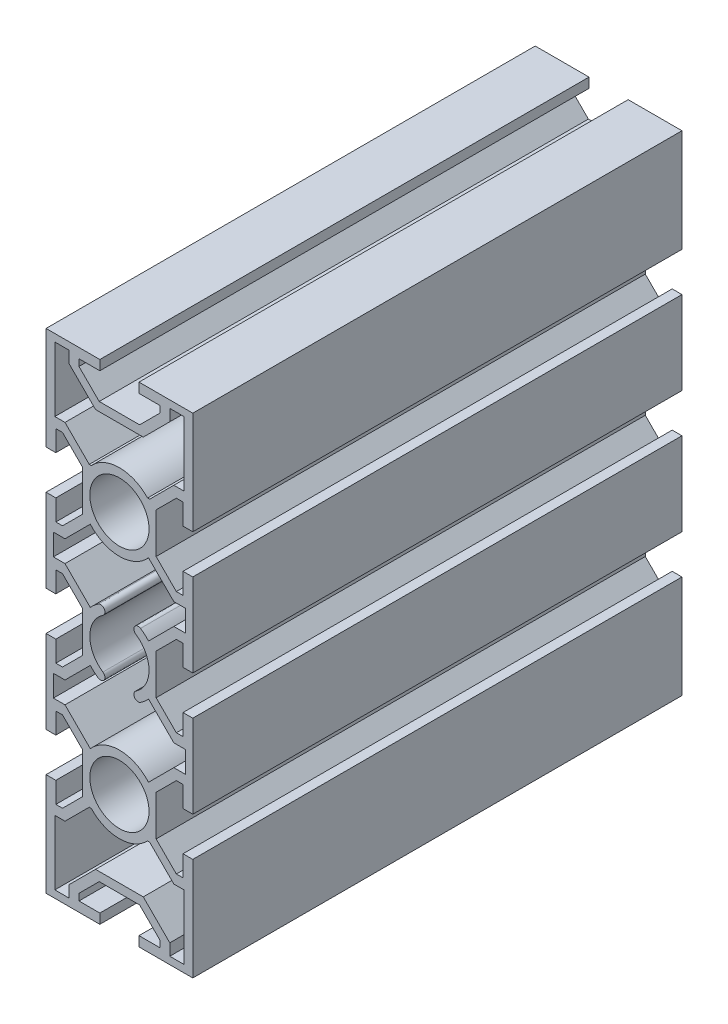
SolidWorks part; units mm, degrees
ref_plane "Front Plane" through (0, 0, 0) normal (0, 0, 1) x (1, 0, 0)
ref_plane "Top Plane" through (0, 0, 0) normal (0, 1, 0) x (1, 0, 0)
ref_plane "Right Plane" through (0, 0, 0) normal (1, 0, 0) x (0, 0, -1)
sketch "MB1-2" plane through (0, 0, 0) normal (0, 0, 1) x (1, 0, 0)
  line L134 (5.7482, -30.3461) -> (6.1691, -30.3461)
  line L135 (-6.1691, -30.3461) -> (-5.7482, -30.3461)
  line L136 (6.1691, 30.3461) -> (5.7482, 30.3461)
  line L137 (-5.7482, 30.3461) -> (-6.1691, 30.3461)
  line L138 (-13, -33.2657) -> (-11.6343, -33.2657)
  line L139 (-11.6343, -16.7343) -> (-13, -16.7343)
  line L140 (-13, -8.2657) -> (-11.6343, -8.2657)
  line L141 (-11.6343, 8.2657) -> (-13, 8.2657)
  line L142 (-13, 16.7343) -> (-11.6343, 16.7343)
  line L143 (-11.6343, 33.2657) -> (-13, 33.2657)
  line L144 (-8.2657, 48) -> (-8.2657, 46.6343)
  line L145 (8.2657, 46.6343) -> (8.2657, 48)
  line L146 (13, 33.2657) -> (11.6343, 33.2657)
  line L147 (11.6343, 16.7343) -> (13, 16.7343)
  line L148 (13, 8.2657) -> (11.6343, 8.2657)
  line L149 (11.6343, -8.2657) -> (13, -8.2657)
  line L150 (13, -16.7343) -> (11.6343, -16.7343)
  line L151 (11.6343, -33.2657) -> (13, -33.2657)
  line L152 (8.2657, -48) -> (8.2657, -46.6343)
  line L153 (-8.2657, -46.6343) -> (-8.2657, -48)
  line L154 (-13.2, -35.3) -> (-13.2, -48.5)
  line L155 (-13.2, -48.5) -> (-10.3, -48.5)
  line L156 (-10.3, -48.5) -> (-10.3, -46.123)
  line L157 (-10.3, -46.123) -> (-4.877, -40.7)
  line L158 (-4.877, -40.7) -> (4.877, -40.7)
  line L159 (4.877, -40.7) -> (10.3, -46.123)
  line L160 (10.3, -46.123) -> (10.3, -48.5)
  line L161 (10.3, -48.5) -> (13.2, -48.5)
  line L162 (13.2, -48.5) -> (13.2, -35.3)
  line L163 (13.2, -35.3) -> (11.123, -35.3)
  line L164 (11.123, -35.3) -> (6.1691, -30.3461)
  line L165 (-6.1691, -30.3461) -> (-11.123, -35.3)
  line L166 (-11.123, -35.3) -> (-13.2, -35.3)
  line L167 (6.1691, 30.3461) -> (11.123, 35.3)
  line L168 (11.123, 35.3) -> (13.2, 35.3)
  line L169 (13.2, 35.3) -> (13.2, 48.5)
  line L170 (13.2, 48.5) -> (10.3, 48.5)
  line L171 (10.3, 48.5) -> (10.3, 46.123)
  line L172 (10.3, 46.123) -> (4.877, 40.7)
  line L173 (4.877, 40.7) -> (-4.877, 40.7)
  line L174 (-4.877, 40.7) -> (-10.3, 46.123)
  line L175 (-10.3, 46.123) -> (-10.3, 48.5)
  line L176 (-10.3, 48.5) -> (-13.2, 48.5)
  line L177 (-13.2, 48.5) -> (-13.2, 35.3)
  line L178 (-13.2, 35.3) -> (-11.123, 35.3)
  line L179 (-11.123, 35.3) -> (-6.1691, 30.3461)
  line L180 (-11.123, -14.7) -> (-5.947, -19.876)
  line L181 (5.947, -19.876) -> (11.123, -14.7)
  line L182 (11.123, -14.7) -> (13.5, -14.7)
  line L183 (13.5, -14.7) -> (13.5, -10.3)
  line L184 (13.5, -10.3) -> (11.123, -10.3)
  line L185 (11.123, -10.3) -> (5.947, -5.124)
  line L186 (5.947, 5.124) -> (11.123, 10.3)
  line L187 (11.123, 10.3) -> (13.5, 10.3)
  line L188 (13.5, 10.3) -> (13.5, 14.7)
  line L189 (13.5, 14.7) -> (11.123, 14.7)
  line L190 (11.123, 14.7) -> (5.947, 19.876)
  line L191 (-5.947, 19.876) -> (-11.123, 14.7)
  line L192 (-11.123, 14.7) -> (-13.5, 14.7)
  line L193 (-13.5, 14.7) -> (-13.5, 10.3)
  line L194 (-13.5, 10.3) -> (-11.123, 10.3)
  line L195 (-11.123, 10.3) -> (-5.947, 5.124)
  line L196 (-5.947, -5.124) -> (-11.123, -10.3)
  line L197 (-11.123, -10.3) -> (-13.5, -10.3)
  line L198 (-13.5, -10.3) -> (-13.5, -14.7)
  line L199 (-13.5, -14.7) -> (-11.123, -14.7)
  line L200 (-15, -29) -> (-13, -29)
  line L201 (-13, -29) -> (-13, -33.2657)
  line L202 (-11.6343, -33.2657) -> (-7.5, -29.1314)
  line L203 (-7.5, -29.1314) -> (-7.5, -20.8686)
  line L204 (-7.5, -20.8686) -> (-11.6343, -16.7343)
  line L205 (-13, -16.7343) -> (-13, -21)
  line L206 (-13, -21) -> (-15, -21)
  line L207 (-15, -21) -> (-15, -4)
  line L208 (-15, -4) -> (-13, -4)
  line L209 (-13, -4) -> (-13, -8.2657)
  line L210 (-11.6343, -8.2657) -> (-7.5, -4.1314)
  line L211 (-7.5, -4.1314) -> (-7.5, 4.1314)
  line L212 (-7.5, 4.1314) -> (-11.6343, 8.2657)
  line L213 (-13, 8.2657) -> (-13, 4)
  line L214 (-13, 4) -> (-15, 4)
  line L215 (-15, 4) -> (-15, 21)
  line L216 (-15, 21) -> (-13, 21)
  line L217 (-13, 21) -> (-13, 16.7343)
  line L218 (-11.6343, 16.7343) -> (-7.5, 20.8686)
  line L219 (-7.5, 20.8686) -> (-7.5, 29.1314)
  line L220 (-7.5, 29.1314) -> (-11.6343, 33.2657)
  line L221 (-13, 33.2657) -> (-13, 29)
  line L222 (-13, 29) -> (-15, 29)
  line L223 (-15, 29) -> (-15, 50)
  line L224 (-15, 50) -> (-4, 50)
  line L225 (-4, 50) -> (-4, 48)
  line L226 (-4, 48) -> (-8.2657, 48)
  line L227 (-8.2657, 46.6343) -> (-4.1314, 42.5)
  line L228 (-4.1314, 42.5) -> (4.1314, 42.5)
  line L229 (4.1314, 42.5) -> (8.2657, 46.6343)
  line L230 (8.2657, 48) -> (4, 48)
  line L231 (4, 48) -> (4, 50)
  line L232 (4, 50) -> (15, 50)
  line L233 (15, 50) -> (15, 29)
  line L234 (15, 29) -> (13, 29)
  line L235 (13, 29) -> (13, 33.2657)
  line L236 (11.6343, 33.2657) -> (7.5, 29.1314)
  line L237 (7.5, 29.1314) -> (7.5, 20.8686)
  line L238 (7.5, 20.8686) -> (11.6343, 16.7343)
  line L239 (13, 16.7343) -> (13, 21)
  line L240 (13, 21) -> (15, 21)
  line L241 (15, 21) -> (15, 4)
  line L242 (15, 4) -> (13, 4)
  line L243 (13, 4) -> (13, 8.2657)
  line L244 (11.6343, 8.2657) -> (7.5, 4.1314)
  line L245 (7.5, 4.1314) -> (7.5, -4.1314)
  line L246 (7.5, -4.1314) -> (11.6343, -8.2657)
  line L247 (13, -8.2657) -> (13, -4)
  line L248 (13, -4) -> (15, -4)
  line L249 (15, -4) -> (15, -21)
  line L250 (15, -21) -> (13, -21)
  line L251 (13, -21) -> (13, -16.7343)
  line L252 (11.6343, -16.7343) -> (7.5, -20.8686)
  line L253 (7.5, -20.8686) -> (7.5, -29.1314)
  line L254 (7.5, -29.1314) -> (11.6343, -33.2657)
  line L255 (13, -33.2657) -> (13, -29)
  line L256 (13, -29) -> (15, -29)
  line L257 (15, -29) -> (15, -50)
  line L258 (15, -50) -> (4, -50)
  line L259 (4, -50) -> (4, -48)
  line L260 (4, -48) -> (8.2657, -48)
  line L261 (8.2657, -46.6343) -> (4.1314, -42.5)
  line L262 (4.1314, -42.5) -> (-4.1314, -42.5)
  line L263 (-4.1314, -42.5) -> (-8.2657, -46.6343)
  line L264 (-8.2657, -48) -> (-4, -48)
  line L265 (-4, -48) -> (-4, -50)
  line L266 (-4, -50) -> (-15, -50)
  line L267 (-15, -50) -> (-15, -29)
  arc A16 (-5.7482, -30.3461) -> (5.7482, -30.3461) centre (0, -25) ccw
  arc A17 (5.7482, 30.3461) -> (-5.7482, 30.3461) centre (0, 25) ccw
  arc A18 (5.947, -19.876) -> (-5.947, -19.876) centre (0, -25) ccw
  arc A19 (4.3175, -6.556) -> (5.947, -5.124) centre (0, 0) ccw
  arc A20 (3.3757, -5.0207) -> (4.3175, -6.556) centre (3.8474, -5.7878) ccw
  arc A21 (3.3757, -5.0207) -> (3.3757, 5.0207) centre (0, 0) ccw
  arc A22 (4.3175, 6.556) -> (3.3757, 5.0207) centre (3.8466, 5.7883) ccw
  arc A23 (5.947, 5.124) -> (4.3175, 6.556) centre (0, 0) ccw
  arc A24 (-5.947, 19.876) -> (5.947, 19.876) centre (0, 25) ccw
  arc A25 (-4.3175, 6.556) -> (-5.947, 5.124) centre (0, 0) ccw
  arc A26 (-3.3757, 5.0207) -> (-4.3175, 6.556) centre (-3.8474, 5.7878) ccw
  arc A27 (-3.3757, 5.0207) -> (-3.3757, -5.0207) centre (0, 0) ccw
  arc A28 (-4.3175, -6.556) -> (-3.3757, -5.0207) centre (-3.8474, -5.7878) ccw
  arc A29 (-5.947, -5.124) -> (-4.3175, -6.556) centre (0, 0) ccw
  circle A30 centre (0, -25) radius 6.05
  circle A31 centre (0, 25) radius 6.05
extrude "Extrude1" add sketch "MB1-2" against normal blind 100
